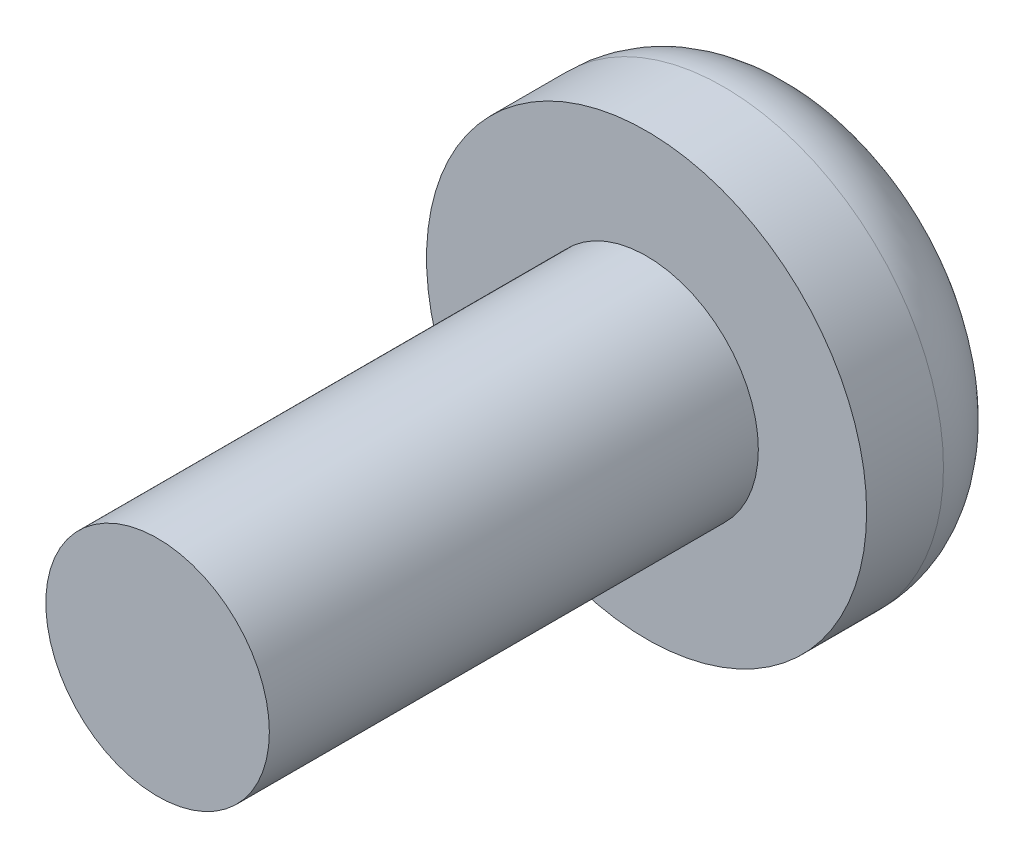
SolidWorks part; units mm, degrees
ref_plane "Front Plane" through (0, 0, 0) normal (0, 0, 1) x (1, 0, 0)
ref_plane "Top Plane" through (0, 0, 0) normal (0, 1, 0) x (1, 0, 0)
ref_plane "Right Plane" through (0, 0, 0) normal (1, 0, 0) x (0, 0, -1)
sketch "Sketch1" plane through (0, 0, 0) normal (0, 0, 1) x (1, 0, 0)
  circle A0 centre (0, 0) radius 4.0005
  dimension "D1" = 8.001
extrude "Extrude1" add sketch "Sketch1" along normal blind 2.921
fillet "Fillet1" radius 1.524 1 edges at (4.0005, 0, 0)
sketch "Sketch2" plane through (0, 0, 2.921) normal (0, 0, 1) x (1, 0, 0)
  circle A0 centre (0, 0) radius 2.032
extrude "Extrude2" add sketch "Sketch2" along normal blind 8.89
sketch "Sketch3" plane through (0, 0, 0) normal (0, 0, -1) x (-1, 0, 0)
  line L1 (2.4573, 0.3079) -> (-2.4573, 0.3079)
  line L2 (2.4573, 0.3079) -> (2.4573, -0.3079)
  line L3 (2.4573, -0.3079) -> (-2.4573, -0.3079)
  line L4 (-2.4573, 0.3079) -> (-2.4573, -0.3079)
  line L5 (2.4573, 0.3079) -> (-2.4573, -0.3079) construction
  line L6 (2.4573, -0.3079) -> (-2.4573, 0.3079) construction
  circle A0 centre (0, 0) radius 2.4765 construction
  point P0 (0, 0)
  point P8 (0, 0)
extrude "Extrude3" cut sketch "Sketch3" against normal blind 1.016
pattern_circular "CirPattern1" count 2 over 90 about axis through (0, 0, 0) along (0, 0, 1) of "Extrude3"
